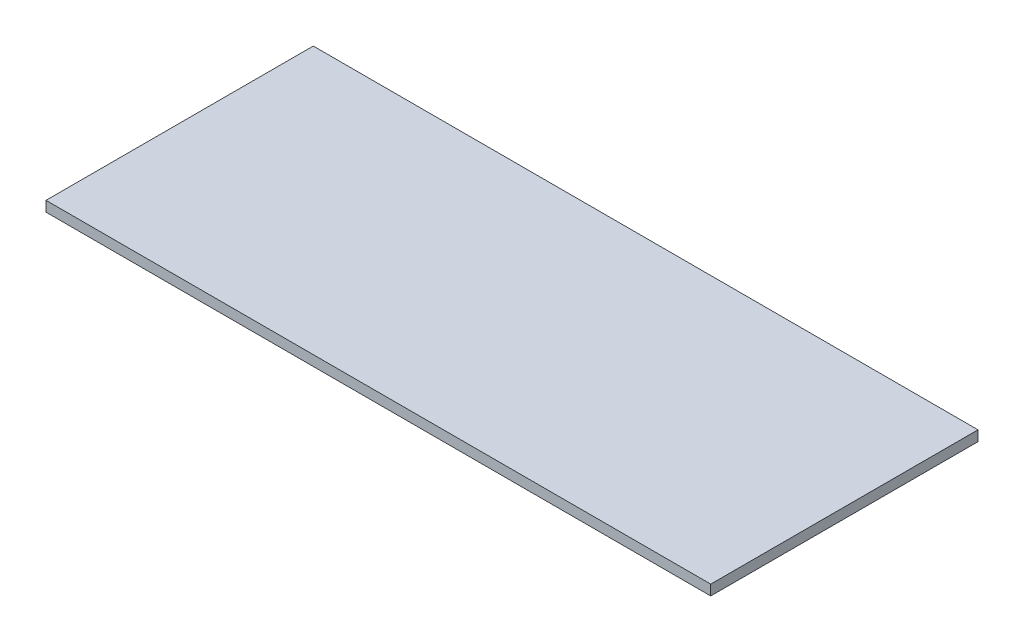
SolidWorks part; units mm, degrees
ref_plane "Front Plane" through (0, 0, 0) normal (0, 0, 1) x (1, 0, 0)
ref_plane "Top Plane" through (0, 0, 0) normal (0, 1, 0) x (1, 0, 0)
ref_plane "Right Plane" through (0, 0, 0) normal (1, 0, 0) x (0, 0, -1)
sketch "Sketch1" plane through (0, 0, 0) normal (0, 1, 0) x (1, 0, 0)
  line L1 (97, -39) -> (-97, -39)
  line L2 (97, -39) -> (97, 39)
  line L3 (97, 39) -> (-97, 39)
  line L4 (-97, -39) -> (-97, 39)
  line L5 (97, -39) -> (-97, 39) construction
  line L6 (97, 39) -> (-97, -39) construction
  point P0 (0, 0)
extrude "Boss-Extrude1" add sketch "Sketch1" along normal blind 3
